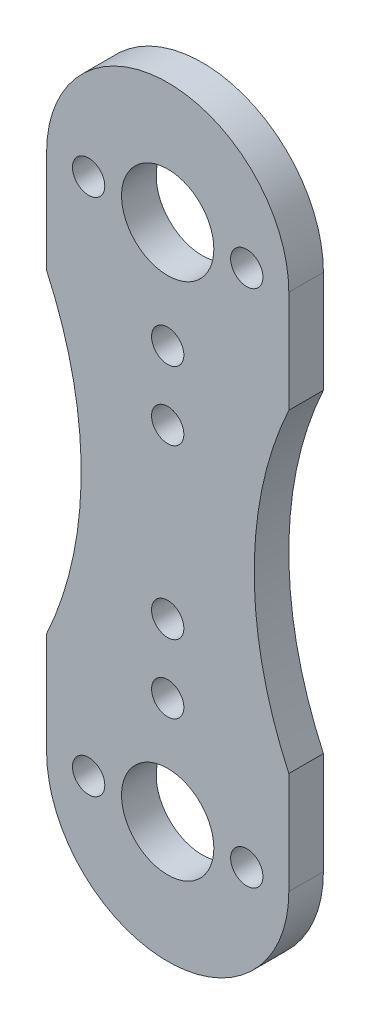
SolidWorks part; units mm, degrees
ref_plane "前视基准面" through (0, 0, 0) normal (0, 0, 1) x (1, 0, 0)
ref_plane "上视基准面" through (0, 0, 0) normal (0, 1, 0) x (1, 0, 0)
ref_plane "右视基准面" through (0, 0, 0) normal (1, 0, 0) x (0, 0, -1)
sketch "草图1" plane through (0, 0, 0) normal (0, 0, 1) x (1, 0, 0)
  line L0 (0, 0) -> (0, 22.5) construction
  line L1 (10.5, -13.6382) -> (10.5, -22.5)
  line L2 (-10.5, 22.5) -> (-10.5, 13.6382)
  line L3 (0, 22.5) -> (6.855, 22.5) construction
  line L4 (10.5, 22.5) -> (10.5, 13.6382)
  line L5 (-10.5, -13.6382) -> (-10.5, -22.5)
  line L7 (0, 0) -> (40, 0) construction
  arc A0 (10.5, 22.5) -> (-10.5, 22.5) centre (0, 22.5) ccw
  arc A1 (10.5, -22.5) -> (-10.5, -22.5) centre (0, -22.5) cw
  arc A2 (10.5, 13.6382) -> (10.5, -13.6382) centre (40, 0) ccw
  arc A3 (-10.5, 13.6382) -> (-10.5, -13.6382) centre (-40, 0) cw
  circle A4 centre (0, 22.5) radius 4
  circle A5 centre (0, -22.5) radius 4
  circle A6 centre (0, 13.23) radius 1.4
  circle A7 centre (6.855, 22.5) radius 1.4
  circle A8 centre (-6.855, 22.5) radius 1.4
  circle A9 centre (0, -7.28) radius 1.4
  circle A10 centre (0, -13.23) radius 1.4
  circle A11 centre (-6.855, -22.5) radius 1.4
  circle A12 centre (0, 7.28) radius 1.4
  circle A13 centre (6.855, -22.5) radius 1.4
  point P0 (0, 0)
  point P16 (0, 19.246)
  dimension "D3" = 21
  dimension "D2" = 65
  dimension "D6" = 8
  dimension "D9" = 2.8
  dimension "D11" = 2.8
  dimension "D8" = 2.8
  dimension "D1" = 21
  dimension "D4" = 45
  dimension "D5" = 40
  dimension "D7" = 9.27
  dimension "D10" = 15.22
  dimension "D12" = 13.71
extrude "凸台-拉伸1" add sketch "草图1" along normal blind 3
